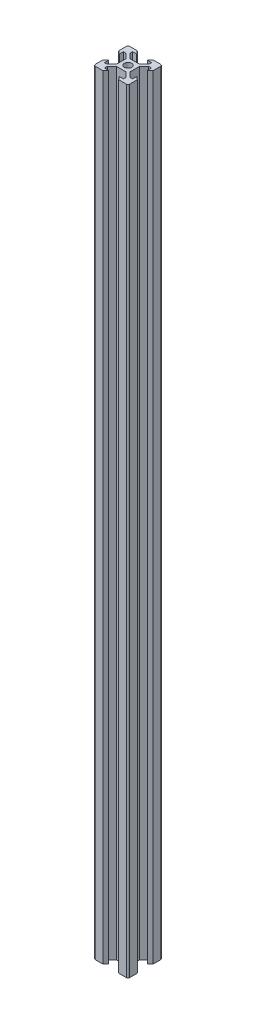
SolidWorks part; units mm, degrees
ref_plane "Front Plane" through (0, 0, 0) normal (0, 0, 1) x (1, 0, 0)
ref_plane "Top Plane" through (0, 0, 0) normal (0, 1, 0) x (1, 0, 0)
ref_plane "Right Plane" through (0, 0, 0) normal (1, 0, 0) x (0, 0, -1)
sketch "Sketch1" plane through (0, 0, 0) normal (0, 1, 0) x (1, 0, 0)
  line L0 (-3.125, 8.2) -> (-4.58, 10)
  line L1 (-9, 10) -> (9, 10)
  line L2 (-10, 9) -> (-10, -9)
  line L3 (-9, -10) -> (9, -10)
  line L4 (10, 9) -> (10, -9)
  line L5 (-10, 10) -> (10, -10) construction
  line L6 (-10, -10) -> (10, 10) construction
  line L7 (-10, 0) -> (0, 0) construction
  line L8 (0, 10) -> (0, 0) construction
  line L9 (-8.2, 3.125) -> (-10, 4.58)
  line L10 (-8.2, 3.125) -> (-8.2, 5.5)
  line L11 (-3.125, 8.2) -> (-5.5, 8.2)
  line L12 (-5.5, 8.2) -> (-5.5, 6.56)
  line L13 (-2.84, 3.9) -> (2.84, 3.9)
  line L14 (-5.5, 6.56) -> (-2.84, 3.9)
  line L15 (-8.2, 5.5) -> (-6.56, 5.5)
  line L16 (-6.56, 5.5) -> (-3.9, 2.84)
  line L17 (-3.9, 2.84) -> (-3.9, -2.84)
  line L18 (3.9, 2.84) -> (3.9, -2.84)
  line L19 (6.56, 5.5) -> (3.9, 2.84)
  line L20 (8.2, 5.5) -> (6.56, 5.5)
  line L21 (8.2, 3.125) -> (8.2, 5.5)
  line L22 (8.2, 3.125) -> (10, 4.58)
  line L23 (3.125, 8.2) -> (4.58, 10)
  line L24 (3.125, 8.2) -> (5.5, 8.2)
  line L25 (5.5, 8.2) -> (5.5, 6.56)
  line L26 (5.5, 6.56) -> (2.84, 3.9)
  line L27 (-8.2, -3.125) -> (-10, -4.58)
  line L28 (-8.2, -3.125) -> (-8.2, -5.5)
  line L29 (-8.2, -5.5) -> (-6.56, -5.5)
  line L30 (-6.56, -5.5) -> (-3.9, -2.84)
  line L31 (8.2, -3.125) -> (10, -4.58)
  line L32 (8.2, -3.125) -> (8.2, -5.5)
  line L33 (8.2, -5.5) -> (6.56, -5.5)
  line L34 (6.56, -5.5) -> (3.9, -2.84)
  line L35 (5.5, -6.56) -> (2.84, -3.9)
  line L36 (5.5, -8.2) -> (5.5, -6.56)
  line L37 (3.125, -8.2) -> (5.5, -8.2)
  line L38 (3.125, -8.2) -> (4.58, -10)
  line L39 (-5.5, -6.56) -> (-2.84, -3.9)
  line L40 (-2.84, -3.9) -> (2.84, -3.9)
  line L41 (-5.5, -8.2) -> (-5.5, -6.56)
  line L42 (-3.125, -8.2) -> (-5.5, -8.2)
  line L43 (-3.125, -8.2) -> (-4.58, -10)
  circle A0 centre (0, 0) radius 2.1
  arc A1 (-10, -9) -> (-9, -10) centre (-9, -9) ccw
  arc A2 (9, -10) -> (10, -9) centre (9, -9) ccw
  arc A3 (9, 10) -> (10, 9) centre (9, 9) cw
  arc A4 (-9, 10) -> (-10, 9) centre (-9, 9) ccw
  point P0 (0, 0)
  point P35 (0, 3.9)
  point P40 (-3.9, 0)
  point P41 (3.9, 0)
  dimension "D3" = 4.2
  dimension "D2" = 1
  dimension "D1" = 20
  dimension "D4" = 6.1
  dimension "D5" = 6.25
  dimension "D6" = 11
  dimension "D7" = 5.68
  dimension "D8" = 9.16
  dimension "D9" = 1.8
extrude "Boss-Extrude1" add sketch "Sketch1" along normal blind 450 contours L43 L42 L41 L39 L40 L35 L36 L37 L38 L3 L4 L31 L32 L33 L34 L18 L19 L20 L21 L22 L1 L23 L24 L25 L26 L13 L14 L12 L11 L0 L2 L9 L10 L15 L16 L17 L30 L29 L28 L27 A0
